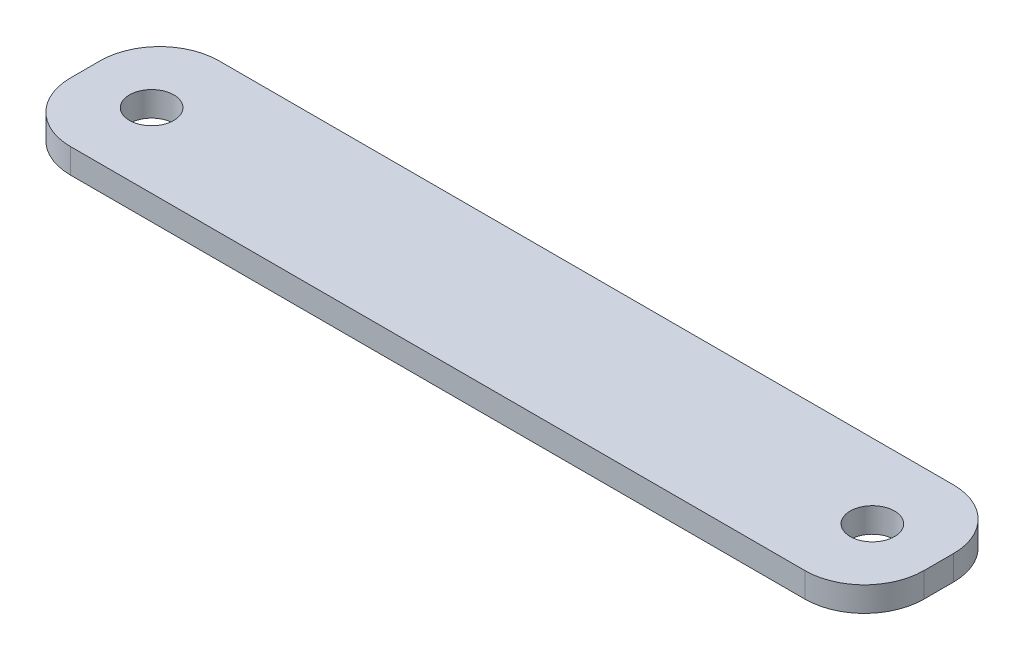
SolidWorks part; units mm, degrees
ref_plane "Front Plane" through (0, 0, 0) normal (0, 0, 1) x (1, 0, 0)
ref_plane "Top Plane" through (0, 0, 0) normal (0, 1, 0) x (1, 0, 0)
ref_plane "Right Plane" through (0, 0, 0) normal (1, 0, 0) x (0, 0, -1)
sketch "Sketch1" plane through (0, 0, 0) normal (0, 1, 0) x (1, 0, 0)
  line L1 (0, 0) -> (54.737, 0)
  line L2 (0, 0) -> (0, 9.525)
  line L3 (0, 9.525) -> (54.737, 9.525)
  line L4 (54.737, 0) -> (54.737, 9.525)
  dimension "D1" = 54.737
  dimension "D2" = 9.525
extrude "Boss-Extrude1" add sketch "Sketch1" along normal blind 1.5875
fillet "Fillet1" radius 3.81 4 edges at (54.737, 0.7937, 0) (54.737, 0.7937, -9.525) (0, 0.7937, -9.525) (0, 0.7937, 0)
sketch "Sketch2" plane through (0, 1.5875, 0) normal (0, 1, 0) x (1, 0, 0)
  line L2 (27.3685, 9.525) -> (27.3685, 0) construction
  line L5 (50.927, 9.525) -> (3.81, 9.525) construction
  line L6 (3.81, 0) -> (50.927, 0) construction
  line L7 (0, 4.7625) -> (54.737, 4.7625) construction
  line L8 (0, 5.715) -> (0, 3.81) construction
  line L9 (54.737, 3.81) -> (54.737, 5.715) construction
  circle A0 centre (4.2545, 4.7625) radius 1.4224
  circle A1 centre (50.4825, 4.7625) radius 1.4224
  dimension "D2" = 2.8448
  dimension "D1" = 46.228
extrude "Cut-Extrude1" cut sketch "Sketch2" against normal through all
ref_point "Point1"
